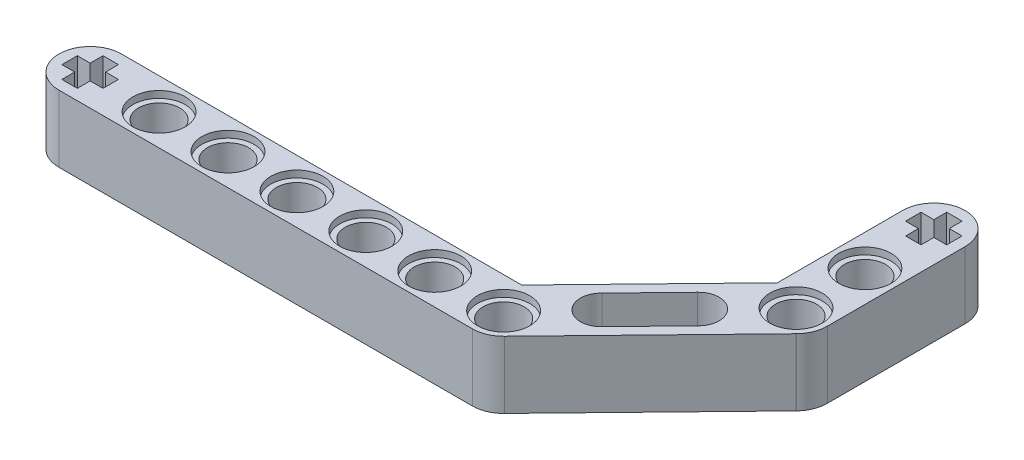
SolidWorks part; units mm, degrees
ref_plane "Front Plane" through (0, 0, 0) normal (0, 0, 1) x (1, 0, 0)
ref_plane "Top Plane" through (0, 0, 0) normal (0, 1, 0) x (1, 0, 0)
ref_plane "Right Plane" through (0, 0, 0) normal (1, 0, 0) x (0, 0, -1)
sketch "Sketch1" plane through (0, 0, 0) normal (0, 1, 0) x (1, 0, 0)
  line L0 (-31.6285, 0) -> (16.6115, 0) construction
  line L1 (-55, 0) -> (55, 0) construction
  line L2 (-31.6285, 3.65) -> (15.067, 3.65)
  line L3 (-31.6285, -3.65) -> (16.6115, -3.65)
  line L4 (16.6115, 0) -> (33.4053, 17.3131) construction
  line L5 (15.067, 3.65) -> (29.7553, 18.7925)
  line L7 (33.4053, 17.3131) -> (33.4053, 33.403) construction
  line L8 (29.7553, 18.7925) -> (29.7553, 33.403)
  line L9 (37.0553, 17.323) -> (37.0553, 33.403)
  line L10 (-31.6285, 0) -> (-31.6285, -13.8031) construction
  line L11 (-23.5885, 0) -> (-23.5885, -12.6804) construction
  line L12 (-15.5485, 0) -> (-15.5485, -12.6804) construction
  line L13 (-7.5085, 0) -> (-7.5085, -14.8282) construction
  line L14 (0.5315, 0) -> (0.5315, -11.6066) construction
  line L15 (8.5715, 0) -> (8.5715, -9.5564) construction
  line L16 (16.6115, 0) -> (16.6115, -15.1699) construction
  line L17 (33.4053, 33.403) -> (45.5605, 33.403) construction
  line L18 (33.4053, 25.363) -> (45.927, 25.363) construction
  line L19 (33.4053, 17.323) -> (42.375, 17.323) construction
  line L20 (22.2094, 5.771) -> (25.7908, 2.2971) construction
  line L21 (27.8074, 11.542) -> (33.4096, 6.1078) construction
  line L22 (-30.7285, 0.9) -> (-29.2285, 0.9)
  line L23 (-32.5285, -2.4) -> (-30.7285, -2.4)
  line L24 (-32.5285, -2.4) -> (-32.5285, -0.9)
  line L25 (-32.5285, 2.4) -> (-30.7285, 2.4)
  line L26 (-30.7285, -2.4) -> (-30.7285, -0.9)
  line L27 (-32.5285, -2.4) -> (-30.7285, 2.4) construction
  line L28 (-32.5285, 2.4) -> (-30.7285, -2.4) construction
  line L29 (-34.0285, -0.9) -> (-32.5285, -0.9)
  line L30 (-34.0285, -0.9) -> (-34.0285, 0.9)
  line L31 (-34.0285, 0.9) -> (-32.5285, 0.9)
  line L32 (-29.2285, -0.9) -> (-29.2285, 0.9)
  line L33 (-34.0285, -0.9) -> (-29.2285, 0.9) construction
  line L34 (-34.0285, 0.9) -> (-29.2285, -0.9) construction
  line L35 (-32.5285, 0.9) -> (-32.5285, 2.4)
  line L36 (-30.7285, 0.9) -> (-30.7285, 2.4)
  line L37 (-30.7285, -0.9) -> (-29.2285, -0.9)
  line L38 (20.5834, 7.5363) -> (26.103, 13.2318)
  line L39 (23.9321, 4.1) -> (29.5301, 9.871)
  line L40 (34.3053, 34.303) -> (35.8053, 34.303)
  line L41 (32.5053, 35.803) -> (34.3053, 35.803)
  line L42 (32.5053, 35.803) -> (32.5053, 34.303)
  line L43 (32.5053, 31.003) -> (34.3053, 31.003)
  line L44 (34.3053, 35.803) -> (34.3053, 34.303)
  line L45 (32.5053, 35.803) -> (34.3053, 31.003) construction
  line L46 (32.5053, 31.003) -> (34.3053, 35.803) construction
  line L47 (31.0053, 32.503) -> (32.5053, 32.503)
  line L48 (31.0053, 32.503) -> (31.0053, 34.303)
  line L49 (31.0053, 34.303) -> (32.5053, 34.303)
  line L50 (35.8053, 32.503) -> (35.8053, 34.303)
  line L51 (31.0053, 32.503) -> (35.8053, 34.303) construction
  line L52 (31.0053, 34.303) -> (35.8053, 32.503) construction
  line L53 (34.3053, 32.503) -> (34.3053, 31.003)
  line L54 (34.3053, 32.503) -> (35.8053, 32.503)
  line L55 (32.5053, 32.503) -> (32.5053, 31.003)
  line L56 (36.0146, 14.7608) -> (35.9795, 14.7249)
  line L57 (35.9795, 14.7249) -> (19.2314, -2.5414)
  arc A0 (-31.6285, 3.65) -> (-31.6285, -3.65) centre (-31.6285, 0) ccw
  arc A1 (16.6115, -3.65) -> (19.2314, -2.5414) centre (16.6115, 0) ccw
  arc A5 (37.0553, 33.403) -> (29.7553, 33.403) centre (33.4053, 33.403) ccw
  circle A6 centre (16.6115, 0) radius 2.4
  circle A7 centre (33.4053, 17.323) radius 0.0069
  circle A8 centre (33.4053, 17.323) radius 2.4
  circle A10 centre (-23.5885, 0) radius 2.4
  circle A11 centre (-15.5485, 0) radius 2.4
  circle A12 centre (-7.5085, 0) radius 2.4
  circle A13 centre (0.5315, 0) radius 2.4
  circle A14 centre (8.5715, 0) radius 2.4
  arc A15 (20.5834, 7.5363) -> (23.9321, 4.1) centre (22.2094, 5.771) ccw
  arc A16 (29.5301, 9.871) -> (26.065, 13.1926) centre (27.8074, 11.542) ccw
  circle A17 centre (33.4053, 25.363) radius 2.4
  arc A18 (36.0146, 14.7608) -> (37.0553, 17.323) centre (33.4053, 17.3131) ccw
  point P5 (-7.5085, 0)
  point P12 (25.0084, 8.6565)
  point P19 (33.4053, 25.358)
  dimension "D14" = 8.04
  dimension "D1" = 7.3
  dimension "D2" = 8.04
  dimension "D4" = 8.04
  dimension "D7" = 8.04
  dimension "D8" = 8.04
  dimension "D9" = 8.04
  dimension "D10" = 8.04
  dimension "D11" = 8.04
  dimension "D12" = 8.04
  dimension "D13" = 8.04
  dimension "D15" = 8.04
extrude "Boss-Extrude1" add sketch "Sketch1" along normal blind 7.8 contours L56 A18 L9 A5 L8 L5 L2 A0 L3 A1 L57 L37 L26 L23 L24 L29 L30 L31 L35 L25 L36 L22 L32 L55 L47 L48 L49 L42 L41 L44 L40 L50 L54 L53 L43 A6 A8 A10 A11 A12 A13 A14
sketch "Sketch2" plane through (0, 7.8, 0) normal (0, 1, 0) x (1, 0, 0)
  circle A0 centre (-23.5885, 0) radius 3.05
  circle A1 centre (-15.5485, 0) radius 3.05
  circle A2 centre (-7.5085, 0) radius 3.05
  circle A3 centre (0.5315, 0) radius 3.05
  circle A4 centre (8.5715, 0) radius 3.05
  circle A5 centre (16.6115, 0) radius 3.05
  circle A6 centre (33.4053, 17.323) radius 3.05
  circle A7 centre (33.4053, 25.363) radius 3.05
extrude "Cut-Extrude1" cut sketch "Sketch2" against normal blind 0.8
sketch "Sketch3" plane through (0, 0, 0) normal (0, -1, 0) x (1, 0, 0)
  line L0 (4.29, 0) -> (-4.29, 0) construction
  circle A0 centre (-23.5597, 0) radius 3.05
  circle A1 centre (-15.5485, 0) radius 3.05
  circle A2 centre (-7.5085, 0) radius 3.05
  circle A3 centre (0.5315, 0) radius 3.05
  circle A4 centre (8.5715, 0) radius 3.05
  circle A5 centre (16.6115, 0) radius 3.05
  circle A6 centre (33.4053, -17.323) radius 3.05
  circle A7 centre (33.4053, -25.363) radius 3.05
extrude "Cut-Extrude2" cut sketch "Sketch3" against normal blind 0.8
